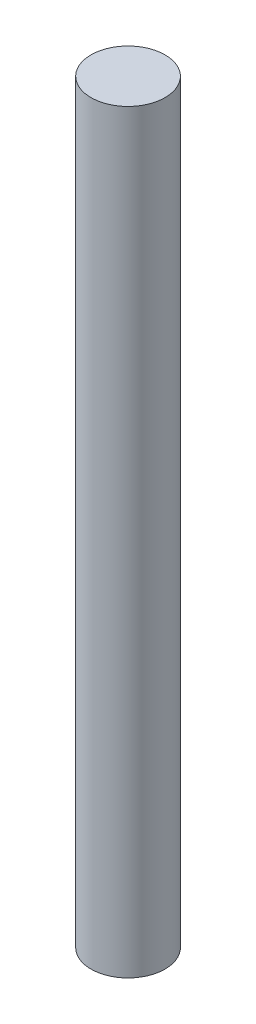
SolidWorks part; units mm, degrees
ref_plane "Piano frontale" through (0, 0, 0) normal (0, 0, 1) x (1, 0, 0)
ref_plane "Piano superiore" through (0, 0, 0) normal (0, 1, 0) x (1, 0, 0)
ref_plane "Piano destro" through (0, 0, 0) normal (1, 0, 0) x (0, 0, -1)
sketch "Sketch1" plane through (0, 0, 0) normal (0, 0, 1) x (1, 0, 0)
  line L0 (4, 41.5) -> (0, 41.5)
  line L1 (0, 41.5) -> (0, -40)
  line L2 (0, -40) -> (4, -40)
  line L3 (4, -40) -> (4, 41.5)
  line L4 (0, 41.5) -> (0, -40) construction
revolve "Revolve1" add sketch "Sketch1" angle 360 about L4
